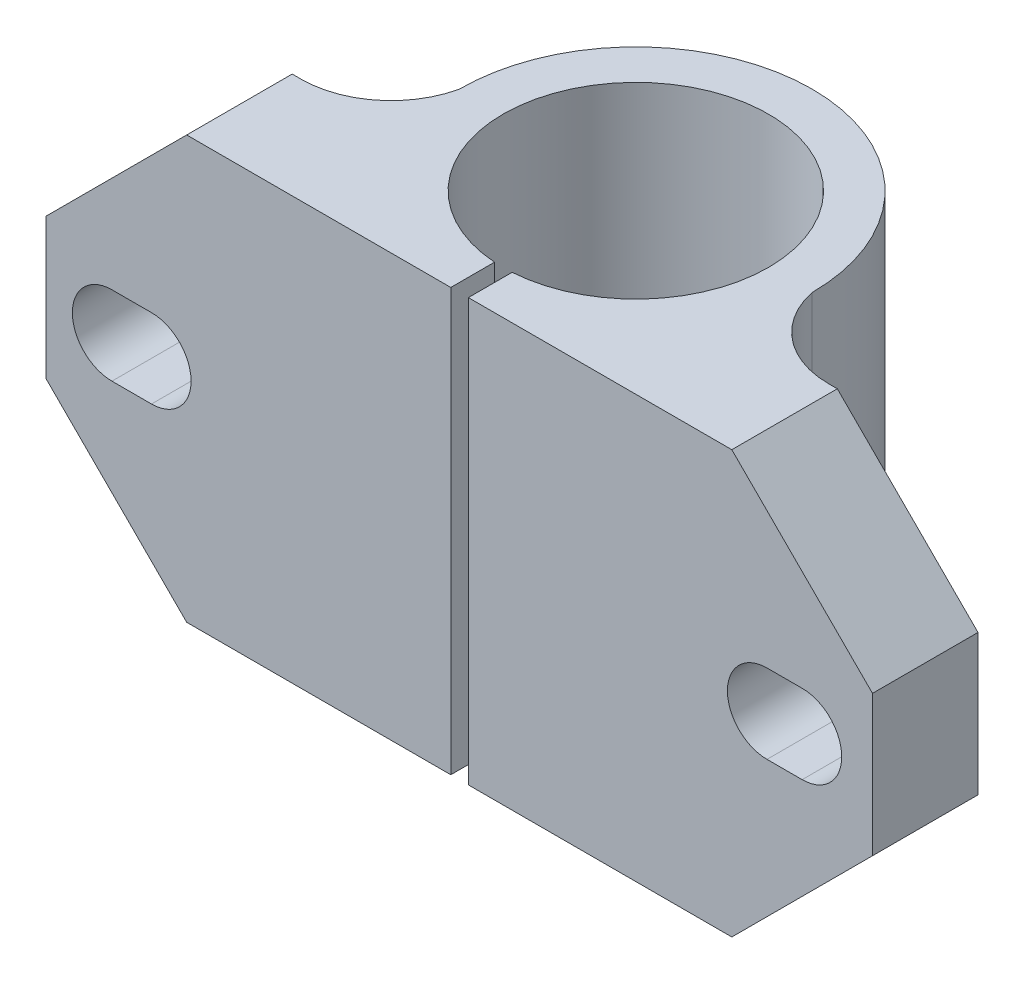
SolidWorks part; units mm, degrees
ref_plane "Front Plane" through (0, 0, 0) normal (0, 0, 1) x (1, 0, 0)
ref_plane "Top Plane" through (0, 0, 0) normal (0, 1, 0) x (1, 0, 0)
ref_plane "Right Plane" through (0, 0, 0) normal (1, 0, 0) x (0, 0, -1)
ref_plane "Plane1" through (0, 24, 0) normal (0, 1, 0) x (1, 0, 0)
sketch "Sketch1" plane through (0, 24, 0) normal (0, 1, 0) x (1, 0, 0)
  line L0 (0, 0) -> (47, 0)
  line L1 (47, 0) -> (47, 6)
  line L2 (47, 6) -> (38.5, 6)
  line L3 (8.5, 6) -> (0, 6)
  line L4 (0, 6) -> (0, 0)
  arc A0 (38.5, 6) -> (33.5414, 10.0218) centre (38.5, 11.0678) cw
  arc A1 (33.5414, 10.0218) -> (13.4959, 9.9961) centre (23.5186, 10.0227) ccw
  arc A2 (13.4959, 9.9961) -> (8.5, 6) centre (8.5, 11.121) cw
extrude "Boss-Extrude1" add sketch "Sketch1" against normal blind 24
sketch "Sketch2" plane through (0, 0, 0) normal (0, -1, 0) x (1, 0, 0)
  line L0 (24.0186, 0) -> (23.0186, 0)
  line L1 (23.0186, 0) -> (23.0186, -2.4893)
  line L2 (24.0186, -2.4893) -> (24.0186, 0)
  arc A0 (23.0186, -2.4893) -> (24.0186, -2.4893) centre (23.5186, -10.0227) cw
extrude "Cut-Extrude1" cut sketch "Sketch2" against normal through all
ref_plane "Plane2" through (0, 0, -10.0227) normal (0, 0, -1) x (-1, 0, 0)
sketch "Sketch3" plane through (0, 0, -10.0227) normal (0, 0, -1) x (-1, 0, 0)
  line L0 (-31.0686, 0) -> (-23.5186, 0)
  line L1 (-23.5186, 0) -> (-23.5186, 24)
  line L2 (-23.5186, 24) -> (-31.0686, 24)
  line L3 (-31.0686, 24) -> (-31.0686, 0)
  line L4 (-23.5186, 0) -> (-23.5186, 24) construction
revolve "Cut-Revolve1" cut sketch "Sketch3" angle 360 about L4
hole_wizard "Ø4.5 (4.5) Diameter Hole1" positions "Sketch5" profile "Sketch4" hole size "Ø4.5" standard "ANSI Metric"
sketch "Sketch5" plane through (0, 0, -6) normal (0, 0, -1) x (-1, 0, 0)
  point P0 (-41.0373, 12)
  point P1 (-6, 12)
  point P2 (0, 0)
sketch "Sketch4" plane through (41.0373, 12, -6) normal (1, 0, 0) x (0, 1, 0)
  line L0 (0, 0) -> (0, 6)
  line L1 (0, 6) -> (2.25, 6)
  line L2 (2.25, 6) -> (2.25, 0)
  line L5 (2.25, 0) -> (0, 0)
  line L11 (0, -6.35) -> (0, 107.95) construction
  dimension "Thru Hole Dia." = 4.5
  dimension "Thru Hole Depth" = 6
chamfer "Chamfer1" distance 8 angle 45 4 edges at (0, 0, -3) (47, 0, -3) (0, 24, -3) (47, 24, -3)
sketch "Sketch7" plane through (0, 0, 0) normal (0, 0, 1) x (1, 0, 0)
  line L1 (0, 12) -> (47, 12) construction
  line L2 (0, 8) -> (0, 16) construction
  line L3 (47, 8) -> (47, 16) construction
  line L4 (41, 12) -> (43, 12) construction
  line L5 (41, 14.25) -> (43, 14.25)
  line L6 (41, 9.75) -> (43, 9.75)
  line L7 (6, 12) -> (3.75, 12) construction
  line L8 (6, 9.75) -> (3.75, 9.75)
  line L9 (6, 14.25) -> (3.75, 14.25)
  arc A0 (41, 14.25) -> (41, 9.75) centre (41, 12) ccw
  arc A1 (43, 9.75) -> (43, 14.25) centre (43, 12) ccw
  circle A2 centre (6, 12) radius 2.25 construction
  arc A3 (6, 9.75) -> (6, 14.25) centre (6, 12) ccw
  arc A4 (3.75, 14.25) -> (3.75, 9.75) centre (3.75, 12) ccw
  point P0 (23.5, 12)
  point P1 (43, 12)
  point P8 (41, 12)
  point P9 (4, 12)
  point P10 (6, 12)
  point P13 (42, 12)
  point P18 (4.875, 12)
  dimension "D5" = 2.25
  dimension "D6" = 2.25
  dimension "D1" = 17.5
  dimension "D2" = 2
  dimension "D3" = 17.5
  dimension "D4" = 2
extrude "Cut-Extrude2" cut sketch "Sketch7" against normal through all
